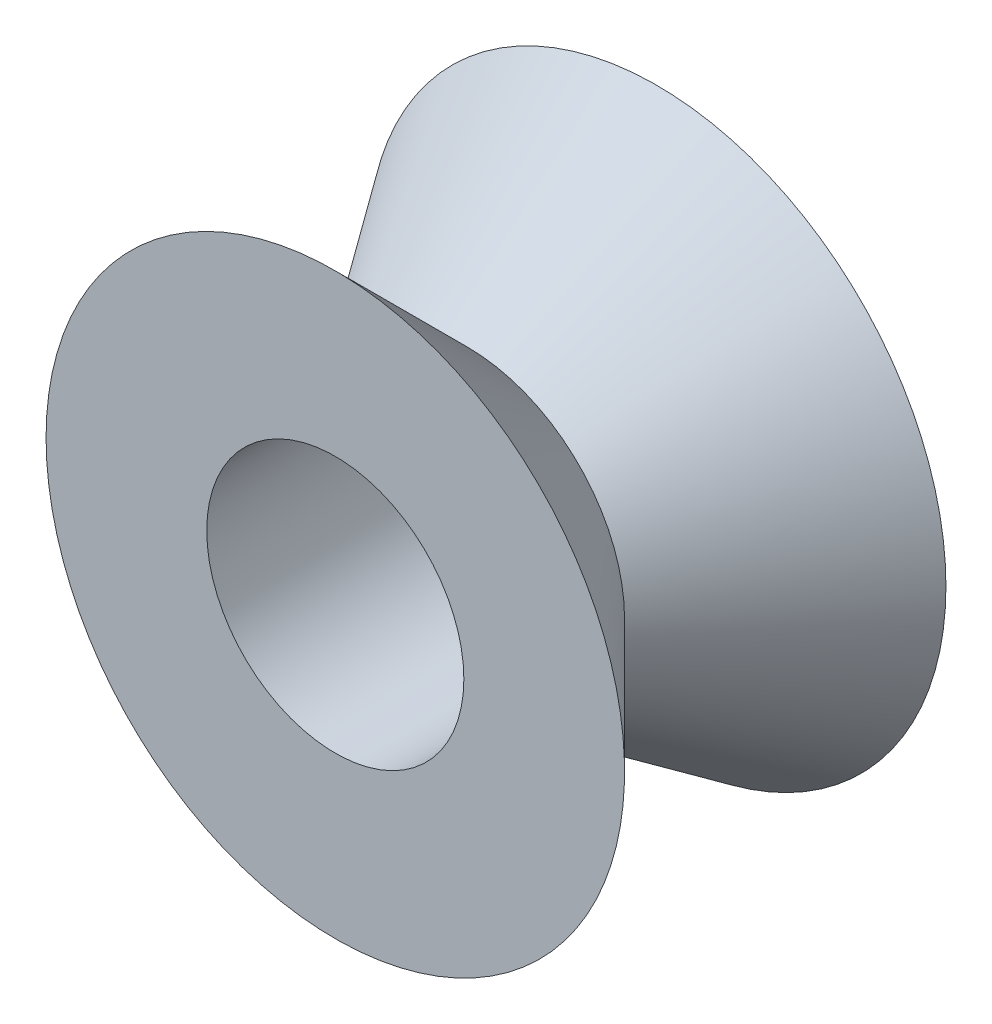
SolidWorks part; units mm, degrees
ref_plane "Front Plane" through (0, 0, 0) normal (0, 0, 1) x (1, 0, 0)
ref_plane "Top Plane" through (0, 0, 0) normal (0, 1, 0) x (1, 0, 0)
ref_plane "Right Plane" through (0, 0, 0) normal (1, 0, 0) x (0, 0, -1)
sketch "Sketch1" plane through (0, 0, 0) normal (0, 0, 1) x (1, 0, 0)
  circle A0 centre (0, 0) radius 9
  dimension "D1" = 18
extrude "Boss-Extrude1" add sketch "Sketch1" along normal blind 10 draft 35
ref_plane "Plane1" through (0, 0, 10) normal (0, 0, -1) x (-1, 0, 0)
sketch "Sketch2" plane through (0, 0, 10) normal (0, 0, -1) x (-1, 0, 0)
  circle A0 centre (0, 0) radius 9
  dimension "D1" = 18
extrude "Boss-Extrude2" add sketch "Sketch2" along normal blind 10 draft 45
sketch "Sketch3" plane through (0, 0, 10) normal (0, 0, -1) x (-1, 0, 0)
  circle A0 centre (0, 0) radius 4
  dimension "D1" = 8
extrude "Cut-Extrude1" cut sketch "Sketch3" along normal blind 20
